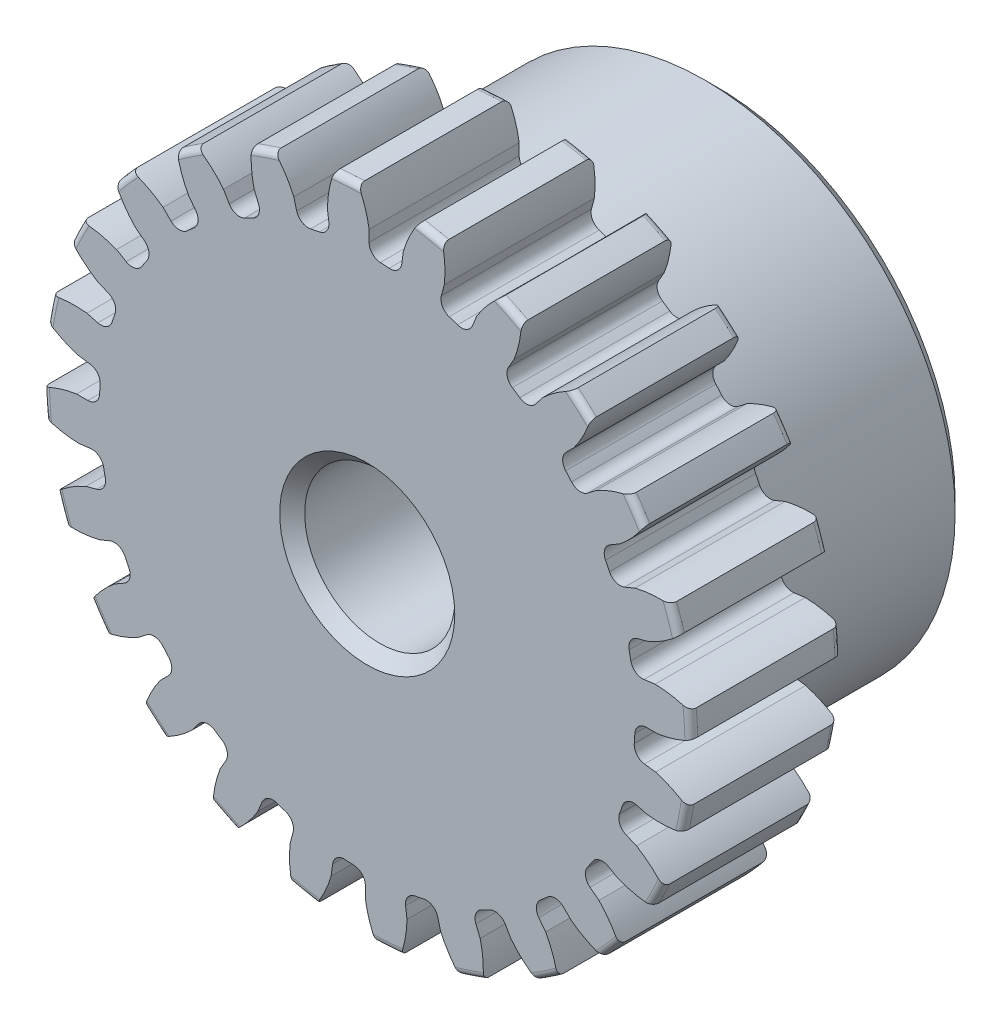
SolidWorks part; units mm, degrees
ref_plane "Front" through (0, 0, 0) normal (0, 0, 1) x (1, 0, 0)
ref_plane "Top" through (0, 0, 0) normal (0, 1, 0) x (1, 0, 0)
ref_plane "Right" through (0, 0, 0) normal (1, 0, 0) x (0, 0, -1)
sketch "Sketch1" plane through (0, 0, 0) normal (0, 0, 1) x (1, 0, 0)
  line L0 (-304.8, 0) -> (304.8, 0) construction
  circle A0 centre (0, 0) radius 10.287
  circle A1 centre (0, 0) radius 9.525 construction
  circle A3 centre (0, 0) radius 8.5011 construction
  dimension "D3" = 0.762
  dimension "D1" = 1.7859
extrude "Boss-Extrude1" add sketch "Sketch1" against normal blind 4.7625
sketch "Sketch2" plane through (0, 0, 0) normal (1, 0, 0) x (0, 0, -1)
  line L0 (4.7625, 0) -> (11.1125, 0)
  line L1 (4.7625, 0) -> (4.7625, 7.9375)
  line L2 (4.7625, 7.9375) -> (11.1125, 7.9375)
  line L3 (11.1125, 7.9375) -> (11.1125, 0)
  point P5 (11.1125, -7.9375)
  point P6 (0, -10.287)
  point P7 (4.7625, -10.287)
  point P9 (0, 10.287)
revolve "Revolve1" add sketch "Sketch2" angle 360 mid plane about L0
fillet "Fillet2" radius 0.2057 3 edges at (10.287, 0, -4.7625) (10.287, 0, 0) (7.9375, 0, -4.7625)
sketch "Sketch3" plane through (0, 0, 0) normal (0, 0, 1) x (1, 0, 0)
  line L0 (0, 0) -> (0, 10.287) construction
  line L1 (-2.3089, 8.9279) -> (0, 9.525)
  line L2 (-9.5921, 9.525) -> (9.5921, 9.525) construction
  line L3 (-9.2865, 7.1233) -> (9.2865, 11.9267) construction
  line L4 (-2.3089, 8.9279) -> (0, 0) construction
  line L5 (-5.8892, 7.0961) -> (0, 0) construction
  line L6 (-5.8892, 7.0961) -> (-0.9538, 11.1922) construction
  line L7 (-1.61, 9.08) -> (0, 0) construction
  line L8 (-1.61, 9.08) -> (0.0338, 9.3714) construction
  arc A0 (-2.3089, 8.9279) -> (-5.8892, 7.0961) centre (0, 0) ccw
  circle A1 centre (0, 0) radius 9.525 construction
  circle A2 centre (0, 0) radius 9.2216 construction
  arc A3 (-2.3089, 8.9279) -> (-1.61, 9.08) centre (0, 0) cw
  circle A4 centre (0, 0) radius 10.287 construction
  point P6 (0, 9.525)
  dimension "D1" = 2.3849
  dimension "D3" = 6.4137
  dimension "D5" = 1.6694
  dimension "D2" = 4.0543
  dimension "D4" = 0.7155
sketch "Sketch4" plane through (0, 0, 0) normal (0, 0, 1) x (1, 0, 0)
  line L0 (0, 0) -> (0.6216, 9.4843) construction
  line L1 (0.0598, 9.2214) -> (0.0598, 8.5009)
  line L2 (0, 9.525) -> (1.2433, 9.4435) construction
  line L3 (1.1444, 9.1503) -> (1.0503, 8.4359)
  line L4 (0.0598, 8.5009) -> (0, 0) construction
  line L5 (0, 0) -> (0, 10.287) construction
  line L6 (-5.8892, 7.0961) -> (-0.9538, 11.1922) construction
  line L7 (-5.8892, 7.0961) -> (-0.9538, 11.1922) construction
  arc A0 (1.0503, 8.4359) -> (0.0598, 8.5009) centre (0, 0) ccw
  arc A1 (0, 9.525) -> (1.2433, 9.4435) centre (0, 0) cw construction
  circle A2 centre (0, 0) radius 9.525 construction
  circle A3 centre (0, 0) radius 9.2216 construction
  circle A4 centre (0, 0) radius 8.5011 construction
  arc A5 (2.4065, 10.9719) -> (-0.9538, 11.1922) centre (0, 0) ccw
  spline S0 degree 2 poles (-0.9538, 11.1922) (-0.1068, 10.325) (0.0598, 9.2214) knots 0 0 0 1 1 1
  spline S1 degree 2 poles (2.4065, 10.9719) (1.4536, 10.2227) (1.1444, 9.1503) knots 0 0 0 1 1 1
  dimension "D1" = 1.2468
extrude "Cut-Extrude1" cut sketch "Sketch4" against normal through all
fillet "Fillet1" radius 0.374 2 edges at (1.0503, 8.4359, -2.3813) (0.0598, 8.5009, -2.3813)
pattern_circular "CirPattern1" count 24 over 360 about axis through (0, 0, -4.7625) along (0, 0, 1) of "Cut-Extrude1", "Fillet1"
sketch "Sketch5" plane through (0, 0, 0) normal (0, 0, 1) x (1, 0, 0)
  circle A0 centre (0, 0) radius 2.3813
  circle A1 centre (0, 0) radius 1.5875 construction
  dimension "Bore Min" = 4.7625
  dimension "Bore Max" = 3.175
extrude "Cut-Extrude2" cut sketch "Sketch5" against normal through all
chamfer "Chamfer1" distance 0.3969 angle 45 3 edges at (7.9375, 0, -11.1125) (2.3813, 0, 0) (2.3813, 0, -11.1125)
sketch "Pitch Dia" plane through (0, 0, 0) normal (0, 0, 1) x (1, 0, 0)
  circle A0 centre (0, 0) radius 9.525 construction
  circle A1 centre (0, 0) radius 9.525 construction
equation "\"D1@Boss-Extrude1\" = \"Face Wd@Sketch2\""
equation "\"D2@Sketch3\" = \"D1@Sketch3\"*1.7"
equation "\"D3@Sketch3\" = \"D1@Sketch3\"+\"D2@Sketch3\"-.001"
equation "\"D4@Sketch3\" = \"D1@Sketch3\"*.3"
equation "\"D5@Sketch3\" = \"D1@Sketch3\"-\"D4@Sketch3\""
equation "\"D1@Sketch4\" = 1.5708/(\"Number of Teeth@Sketch1\"/\"Ptich Dia@Sketch1\")"
equation "\"D1@Chamfer1\" = \"B Hub Dia@Sketch2\"*.025"
equation "\"D1@CirPattern1\" = \"Number of Teeth@Sketch1\""
equation "\"D1@Fillet1\" = \"D1@Sketch4\"*.3"
equation "\"D1@Fillet2\" = \"OD@Sketch1\"*.01"
equation "\"D1@Sketch1\" = 2.250/(\"Number of Teeth@Sketch1\"/\"Ptich Dia@Sketch1\")"
